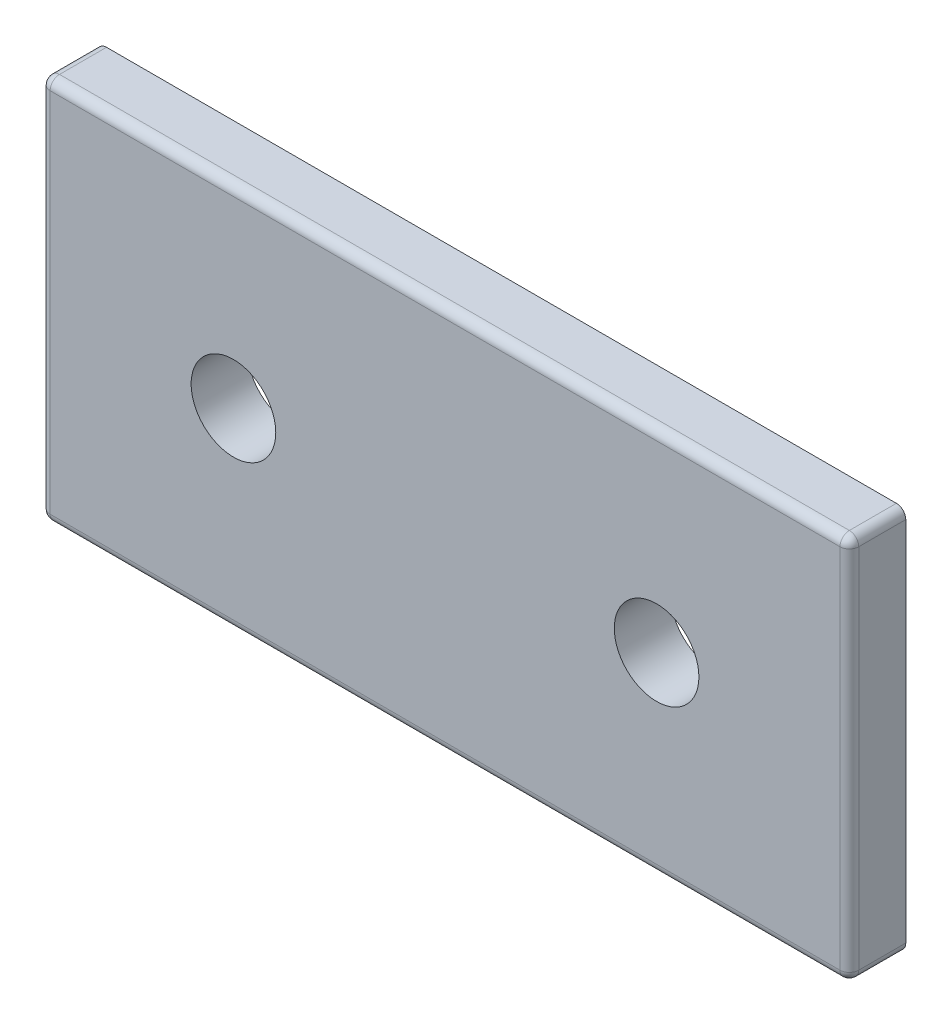
SolidWorks part; units mm, degrees
ref_plane "Front Plane" through (0, 0, 0) normal (0, 0, 1) x (1, 0, 0)
ref_plane "Top Plane" through (0, 0, 0) normal (0, 1, 0) x (1, 0, 0)
ref_plane "Right Plane" through (0, 0, 0) normal (1, 0, 0) x (0, 0, -1)
sketch "Sketch1" plane through (0, 0, 0) normal (0, 0, 1) x (1, 0, 0)
  line L0 (0, 0) -> (0, 41)
  line L1 (20.5, 20.5) -> (65.5, 20.5) construction
  line L4 (86, 41) -> (0, 41)
  line L5 (86, 0) -> (0, 0)
  line L7 (86, 41) -> (86, 0)
  circle A0 centre (20.5, 20.5) radius 4.5
  circle A1 centre (65.5, 20.5) radius 4.5
  dimension "D1" = 45
  dimension "E" = 9
  dimension "D2" = 20.5
  dimension "C" = 41
  dimension "D3" = 20.5
  dimension "B" = 86
extrude "Boss-Extrude1" add sketch "Sketch1" along normal mid plane 6
fillet "Fillet1" radius 1 8 edges at (0, 0, 0) (0, 20.5, 3) (43, 0, 3) (86, 20.5, 3) (86, 0, 0) (86, 41, 0) (43, 41, 3) (0, 41, 0)
